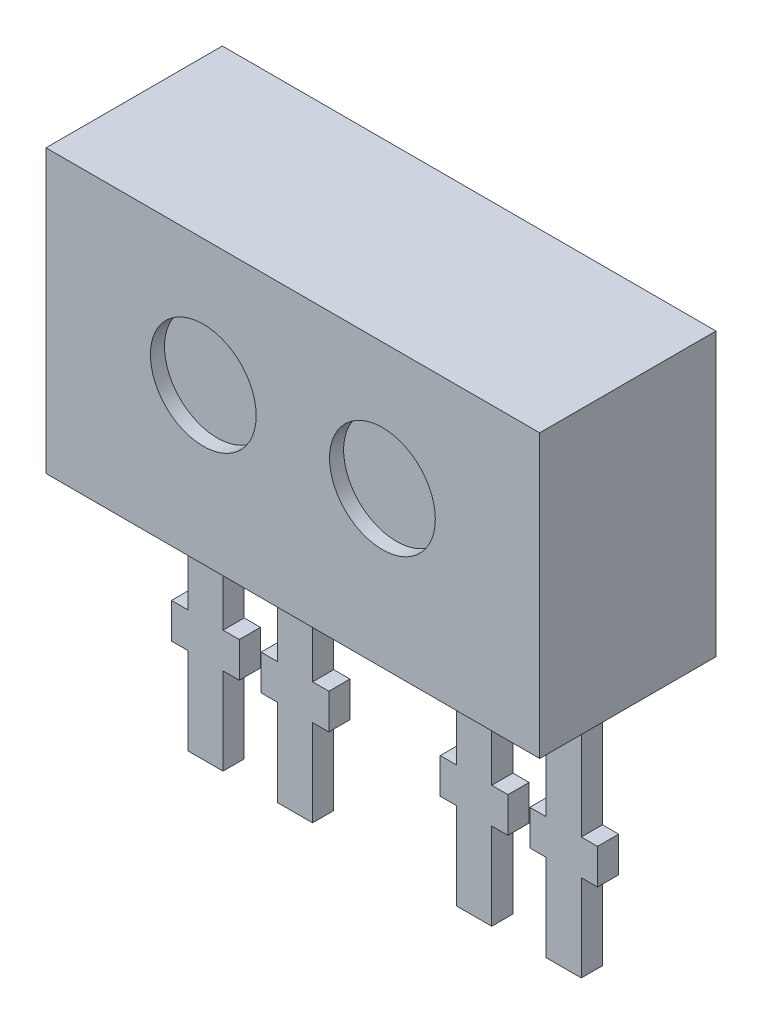
SolidWorks part; units mm, degrees
ref_plane "Front Plane" through (0, 0, 0) normal (0, 0, 1) x (1, 0, 0)
ref_plane "Top Plane" through (0, 0, 0) normal (0, 1, 0) x (1, 0, 0)
ref_plane "Right Plane" through (0, 0, 0) normal (1, 0, 0) x (0, 0, -1)
sketch "Sketch1" plane through (0, 0, 0) normal (0, 0, 1) x (1, 0, 0)
  line L0 (-1.27, 0) -> (1.27, 0) construction
  line L1 (-3.5, -2) -> (3.5, -2)
  line L2 (-3.5, -2) -> (-3.5, 2)
  line L3 (-3.5, 2) -> (3.5, 2)
  line L4 (3.5, -2) -> (3.5, 2)
  line L5 (-3.5, -2) -> (3.5, 2) construction
  line L6 (-3.5, 2) -> (3.5, -2) construction
  circle A0 centre (-1.27, 0) radius 0.5 construction
  circle A1 centre (1.27, 0) radius 0.5 construction
  point P0 (0, 0)
  dimension "D2" = 1
  dimension "D1" = 2.54
  dimension "D3" = 7
  dimension "D4" = 4
extrude "Boss-Extrude1" add sketch "Sketch1" along normal blind 2.5
sketch "Sketch2" plane through (0, 0, 2.5) normal (0, 0, 1) x (1, 0, 0)
  line L0 (-1.27, 0.2) -> (1.27, 0.2) construction
  line L1 (0, 0) -> (0, 0.2) construction
  line L2 (3.5, 2) -> (-3.5, 2) construction
  circle A0 centre (-1.27, 0.2) radius 0.75
  circle A1 centre (1.27, 0.2) radius 0.75
  dimension "D2" = 1.5
  dimension "D1" = 2.54
  dimension "D3" = 1.8
extrude "Cut-Extrude1" cut sketch "Sketch2" against normal blind 0.2
sketch "Sketch3" plane through (0, 0, 0) normal (1, 0, 0) x (0, 0, -1)
  line L0 (-1.2, -2) -> (-1.2, -5.7)
  line L1 (-2.5, -2) -> (0, -2) construction
  line L2 (-1.2, -5.7) -> (-0.9, -5.7)
  line L3 (-2.5, 2) -> (0, 2) construction
  line L5 (-0.9, -5.7) -> (-0.9, -2)
  line L6 (-1.2, -2) -> (-0.9, -2)
  line L10 (-2.5, -2) -> (-2.5, 2) construction
  dimension "D1" = 0.3
  dimension "D2" = 7.7
  dimension "D3" = 1.3
extrude "Boss-Extrude2" add sketch "Sketch3" along normal through all and the other way through all
sketch "Sketch4" plane through (0, 0, 0) normal (0, 0, 1) x (1, 0, 0)
  line L0 (-3.5, -2) -> (3.5, -2) construction
  line L1 (-2.79, -6.0684) -> (-2.29, -6.0684) construction
  line L2 (-2.79, -6.0684) -> (-2.79, -4.4684)
  line L3 (-2.79, -2) -> (-2.29, -2) construction
  line L4 (-2.29, -6.0684) -> (-2.29, -4.4684)
  line L5 (-2.79, -6.0684) -> (-2.29, -2) construction
  line L6 (-2.79, -2) -> (-2.29, -6.0684) construction
  line L7 (0, 0) -> (0, -6.0684) construction
  line L8 (-1.02, -2) -> (1.02, -2)
  line L9 (-1.02, -6.0684) -> (1.02, -6.0684)
  line L10 (-2.29, -6.0684) -> (-1.52, -6.0684)
  line L11 (-2.29, -2) -> (-1.52, -2)
  line L12 (-2.79, -2) -> (-4.1361, -2)
  line L13 (-4.1361, -2) -> (-4.1361, -6.0684)
  line L14 (-1.52, -6.0684) -> (-1.02, -6.0684) construction
  line L15 (-1.52, -6.0684) -> (-1.52, -4.4684)
  line L16 (-1.52, -2) -> (-1.02, -2) construction
  line L17 (-1.02, -6.0684) -> (-1.02, -4.4684)
  line L18 (-1.52, -6.0684) -> (-1.02, -2) construction
  line L19 (-1.52, -2) -> (-1.02, -6.0684) construction
  line L20 (-4.1361, -6.0684) -> (-2.79, -6.0684)
  line L21 (1.52, -2) -> (1.02, -6.0684) construction
  line L22 (1.52, -6.0684) -> (1.02, -2) construction
  line L23 (1.52, -2) -> (1.02, -2) construction
  line L24 (1.52, -6.0684) -> (1.02, -6.0684) construction
  line L25 (2.79, -2) -> (2.29, -6.0684) construction
  line L26 (2.79, -6.0684) -> (2.29, -2) construction
  line L27 (2.79, -2) -> (2.29, -2) construction
  line L28 (2.79, -6.0684) -> (2.29, -6.0684) construction
  line L29 (4.1361, -6.0684) -> (2.79, -6.0684)
  line L30 (1.02, -6.0684) -> (1.02, -4.4684)
  line L31 (1.52, -6.0684) -> (1.52, -4.4684)
  line L32 (4.1361, -2) -> (4.1361, -6.0684)
  line L33 (2.79, -2) -> (4.1361, -2)
  line L34 (2.29, -2) -> (1.52, -2)
  line L35 (2.29, -6.0684) -> (1.52, -6.0684)
  line L36 (2.29, -6.0684) -> (2.29, -4.4684)
  line L37 (2.79, -6.0684) -> (2.79, -4.4684)
  line L38 (-2.29, -4.4684) -> (-2.0599, -4.4684)
  line L39 (-2.0599, -4.4684) -> (-2.0599, -3.9684)
  line L40 (-2.0599, -3.9684) -> (-2.29, -3.9684)
  line L41 (-2.79, -4.4684) -> (-3.0201, -4.4684)
  line L42 (-3.0201, -4.4684) -> (-3.0201, -3.9684)
  line L43 (-3.0201, -3.9684) -> (-2.79, -3.9684)
  line L44 (-1.52, -3.9684) -> (-1.7501, -3.9684)
  line L45 (-1.7501, -3.9684) -> (-1.7501, -4.4684)
  line L46 (-1.7501, -4.4684) -> (-1.52, -4.4684)
  line L47 (-1.02, -3.9684) -> (-0.7899, -3.9684)
  line L48 (-0.7899, -3.9684) -> (-0.7899, -4.4684)
  line L49 (-0.7899, -4.4684) -> (-1.02, -4.4684)
  line L50 (-2.79, -3.9684) -> (-2.79, -2)
  line L51 (-2.29, -3.9684) -> (-2.29, -2)
  line L52 (-1.52, -3.9684) -> (-1.52, -2)
  line L53 (-1.02, -3.9684) -> (-1.02, -2)
  line L54 (0.7899, -4.4684) -> (1.02, -4.4684)
  line L55 (0.7899, -3.9684) -> (0.7899, -4.4684)
  line L56 (1.02, -3.9684) -> (0.7899, -3.9684)
  line L57 (1.7501, -4.4684) -> (1.52, -4.4684)
  line L58 (1.7501, -3.9684) -> (1.7501, -4.4684)
  line L59 (1.52, -3.9684) -> (1.7501, -3.9684)
  line L60 (3.0201, -3.9684) -> (2.79, -3.9684)
  line L61 (3.0201, -4.4684) -> (3.0201, -3.9684)
  line L62 (2.79, -4.4684) -> (3.0201, -4.4684)
  line L63 (2.0599, -3.9684) -> (2.29, -3.9684)
  line L64 (2.0599, -4.4684) -> (2.0599, -3.9684)
  line L65 (2.29, -4.4684) -> (2.0599, -4.4684)
  line L66 (1.02, -3.9684) -> (1.02, -2)
  line L67 (1.52, -3.9684) -> (1.52, -2)
  line L68 (2.29, -3.9684) -> (2.29, -2)
  line L69 (2.79, -3.9684) -> (2.79, -2)
  point P0 (-2.54, -4.0342)
  point P10 (1.27, -4.0342)
  point P12 (-1.27, -4.0342)
  point P29 (0, -2)
  point P30 (2.54, -4.0342)
  dimension "D1" = 0.5
  dimension "D2" = 2.54
  dimension "D3" = 1.27
  dimension "D4" = 1.6
  dimension "D5" = 0.5
extrude "Cut-Extrude2" cut sketch "Sketch4" against normal through all and the other way through all
